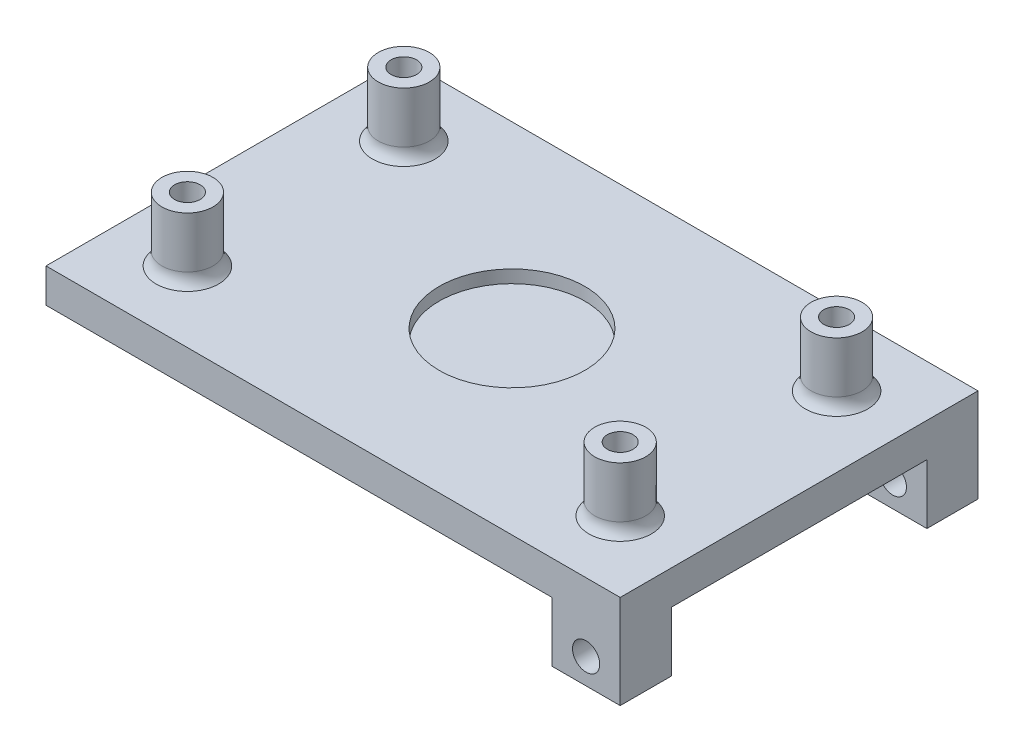
SolidWorks part; units mm, degrees
ref_plane "Front Plane" through (0, 0, 0) normal (0, 0, 1) x (1, 0, 0)
ref_plane "Top Plane" through (0, 0, 0) normal (0, 1, 0) x (1, 0, 0)
ref_plane "Right Plane" through (0, 0, 0) normal (1, 0, 0) x (0, 0, -1)
sketch "Sketch2" plane through (0, 0, 0) normal (0, 1, 0) x (1, 0, 0)
  line L1 (0, 0) -> (75.4, 0)
  line L2 (0, 0) -> (0, 50)
  line L3 (0, 50) -> (75.4, 50)
  line L4 (75.4, 0) -> (75.4, 50)
  dimension "D1" = 50
  dimension "D2" = 75.4
extrude "Boss-Extrude1" add sketch "Sketch2" along normal blind 3.5
sketch "Sketch3" plane through (0, 3.5, 0) normal (0, 1, 0) x (1, 0, 0)
  line L0 (0, 50) -> (0, 0) construction
  line L1 (75.4, 0) -> (75.4, 50) construction
  circle A0 centre (12.3, 37.7) radius 1.5
  circle A1 centre (12.3, 12.3) radius 1.5
  circle A2 centre (63.1, 37.7) radius 1.5
  circle A3 centre (63.1, 12.3) radius 1.5
  point P4 (0, 25)
  point P19 (75.4, 25)
  dimension "D1" = 3
  dimension "D3" = 12.7
  dimension "D4" = 0
  dimension "D5" = 50.8
  dimension "D2" = 0
  dimension "D6" = 12.7
  dimension "D7" = 12.7
extrude "Cut-Extrude1" cut sketch "Sketch3" against normal blind 4
sketch "Sketch4" plane through (0, 3.5, 0) normal (0, 1, 0) x (1, 0, 0)
  circle A0 centre (12.3, 37.7) radius 1.5
  circle A1 centre (12.3, 37.7) radius 3
  dimension "D1" = 6
extrude "Boss-Extrude2" add sketch "Sketch4" along normal blind 8
ref_plane "Plane1" through (37.7, 0, 0) normal (-1, 0, 0) x (0, 0, 1)
ref_plane "Plane2" through (0, 0, -25) normal (0, 0, 1) x (1, 0, 0)
mirror "Mirror1" about plane through (0, 0, -25) normal (0, 0, 1) of "Boss-Extrude2"
mirror "Mirror2" about plane through (37.7, 0, 0) normal (-1, 0, 0) of "Mirror1", "Boss-Extrude2"
fillet "Fillet1" radius 2 4 edges at (63.1, 3.5, -15.3) (63.1, 3.5, -34.7) (12.3, 3.5, -40.7) (12.3, 3.5, -15.3)
sketch "Sketch6" plane through (0, 0, 0) normal (0, -1, 0) x (1, 0, 0)
  line L4 (0, 0) -> (0, -50)
  line L5 (0, -50) -> (75.4, -50)
  line L6 (75.4, -50) -> (75.4, 0)
  line L7 (75.4, 0) -> (0, 0)
  line L8 (0, 0) -> (0, -50)
  line L9 (0, -50) -> (75.4, -50)
  line L10 (75.4, -50) -> (75.4, 0)
  line L11 (75.4, 0) -> (0, 0)
  dimension "D1" = 0
extrude "Boss-Extrude3" add sketch "Sketch6" against normal blind 4
sketch "Sketch8" plane through (0, 0, 0) normal (0, -1, 0) x (1, 0, 0)
  line L0 (37.7, 3.025) -> (37.7, -3.025) construction
  line L1 (8.7, -30) -> (12.7, -30)
  line L2 (8.7, -30) -> (8.7, -45)
  line L3 (8.7, -45) -> (12.7, -45)
  line L4 (12.7, -30) -> (12.7, -45)
  line L5 (12.7, -45) -> (62.7, -45)
  line L6 (12.7, -45) -> (12.7, -41)
  line L7 (12.7, -41) -> (62.7, -41)
  line L8 (62.7, -45) -> (62.7, -41)
  line L9 (3.025, -25) -> (-3.025, -25) construction
  dimension "D1" = 4
  dimension "D2" = 4
  dimension "D3" = 15
  dimension "D4" = 50
  dimension "D5" = 25
  dimension "D6" = 16
extrude "Boss-Extrude4" [suppressed] add sketch "Sketch8" along normal blind 6 contours L5 L8 L7 L6 | L3 L2 L1 L4
fillet "Fillet2" [suppressed] radius 1
fillet "Fillet3" [suppressed] radius 1
mirror "Mirror3" [suppressed] about plane through (0, 0, -25) normal (0, 0, 1)
sketch "Sketch9" plane through (0, 4, 0) normal (0, 1, 0) x (1, 0, 0)
  line L0 (37.7, 50) -> (37.7, 0) construction
  line L3 (0, 50) -> (75.4, 50) construction
  line L4 (75.4, 0) -> (0, 0) construction
  circle A0 centre (37.7, 25) radius 8.55
  dimension "D1" = 17.1
extrude "Cut-Extrude2" cut sketch "Sketch9" against normal blind 1.5
sketch "Sketch10" plane through (0, 0, 0) normal (0, -1, 0) x (1, 0, 0)
  line L0 (0, -25) -> (75.4, -25) construction
  line L1 (0, -50) -> (0, 0) construction
  line L2 (75.4, 0) -> (75.4, -50) construction
  circle A0 centre (17.6997, -25) radius 4.85
  dimension "D1" = 9.7
extrude "Cut-Extrude3" cut sketch "Sketch10" against normal blind 1.87
sketch "Sketch11" plane through (0, 1.87, 0) normal (0, -1, 0) x (1, 0, 0)
  circle A0 centre (17.6997, -25) radius 4
  dimension "D1" = 8
extrude "Cut-Extrude4" cut sketch "Sketch11" against normal blind 0.5
sketch "Sketch12" plane through (0, 0, 0) normal (0, -1, 0) x (1, 0, 0)
  line L0 (0, -50) -> (0, 0) construction
  line L1 (0, -27.5) -> (12.8497, -27.5)
  line L2 (0, -27.5) -> (0, -22.5)
  line L3 (0, -22.5) -> (12.8497, -22.5)
  line L4 (12.8497, -27.5) -> (12.8497, -22.5)
  line L5 (12.8497, -27.5) -> (13.5437, -27.5)
  line L6 (12.8497, -22.5) -> (13.5437, -22.5)
  circle A0 centre (17.6997, -25) radius 4.85 construction
  circle A1 centre (17.6997, -25) radius 4.85
  point P6 (0, -25)
  circle M5 centre (17.6997, -25) radius 4.85
  line M6 (0, 0) -> (0, -50)
  dimension "D1" = 2.5
  dimension "D2" = 5
extrude "Cut-Extrude6" cut sketch "Sketch12" against normal blind 1.87 contours L4 L5 M5 | L6 L4 M5 | L1 L4 L3 M6
sketch "Sketch13" [suppressed] plane through (0, 0, 0) normal (0, -1, 0) x (1, 0, 0)
  line L0 (12.7, -41) -> (61.7, -41) construction
  line L1 (23.4, -41) -> (75.4, -41)
  line L2 (23.4, -41) -> (23.4, -9)
  line L3 (23.4, -9) -> (75.4, -9)
  line L4 (75.4, -41) -> (75.4, -9)
  line L5 (75.4, 0) -> (75.4, -50) construction
  line L6 (12.7, -9) -> (61.7, -9) construction
  dimension "D1" = 52
extrude "Boss-Extrude5" [suppressed] add sketch "Sketch13" along normal blind 0.25
sketch "Sketch14" plane through (0, 0, 0) normal (0, -1, 0) x (1, 0, 0)
  line L1 (63.4, -4) -> (71.4, -4)
  line L2 (63.4, -4) -> (63.4, -10)
  line L3 (63.4, -10) -> (71.4, -10)
  line L4 (71.4, -4) -> (71.4, -10)
  line L6 (0, 0) -> (75.4, 0) construction
  line L7 (75.4, 0) -> (75.4, -50) construction
  dimension "D1" = 6
  dimension "D2" = 8
  dimension "D3" = 4
  dimension "D4" = 4
extrude "Boss-Extrude6" add sketch "Sketch14" along normal blind 8
sketch "Sketch15" plane through (0, 0, -10) normal (0, 0, -1) x (-1, 0, 0)
  line L0 (-67.4, -8) -> (-67.4, 0) construction
  line L1 (-63.4, -8) -> (-71.4, -8) construction
  line L2 (-63.4, 0) -> (-71.4, 0) construction
  circle A0 centre (-67.4, -4) radius 1.6
  dimension "D1" = 3.2
extrude "Cut-Extrude7" cut sketch "Sketch15" against normal blind 8
mirror "Mirror4" about plane through (0, 0, -25) normal (0, 0, 1) of "Cut-Extrude7", "Boss-Extrude6"
sketch "Sketch16" plane through (0, 0, 0) normal (0, -1, 0) x (1, 0, 0)
  line L51 (0, -50) -> (0, -27.5) construction
  line L52 (71.4, -4) -> (4, -4)
  line L53 (71.4, -4) -> (71.4, -46)
  line L54 (71.4, -46) -> (4, -46)
  line L55 (4, -4) -> (4, -46)
  line L56 (71.4, -4) -> (4, -46) construction
  line L57 (71.4, -46) -> (4, -4) construction
  line L58 (75.4, -50) -> (0, -50) construction
  line L59 (75.4, -50) -> (0, -50) construction
  line L60 (0, 0) -> (4, 0)
  line L61 (0, 0) -> (0, -50)
  line L62 (0, -50) -> (4, -50)
  line L63 (4, 0) -> (4, -50)
  point P69 (37.7, -25)
  line M7 (71.4, -40) -> (71.4, -46)
  line M8 (0, -50) -> (75.4, -50)
  line M9 (75.4, -50) -> (75.4, 0)
  line M11 (71.4, -4) -> (71.4, -10)
  line M14 (75.4, 0) -> (0, 0)
  line M15 (0, 0) -> (0, -22.5)
  line M16 (0, -22.5) -> (13.5437, -22.5)
  line M18 (13.5437, -27.5) -> (0, -27.5)
  line M19 (0, -27.5) -> (0, -50)
  line M25 (71.4, -46) -> (63.4, -46)
  line M26 (63.4, -4) -> (71.4, -4)
  dimension "D1" = 4
  dimension "D2" = 4
extrude "Cut-Extrude8" cut sketch "Sketch16" against normal blind 8 contours L63 L55 M18 M19 M8 | L61 L55 M16 M18 | L63 L55 M14 M15 M16 | L63 L52 L53 L54 M14 M26 M11 M7 M25 M8 M9
sketch "Sketch17" plane through (0, -8, 0) normal (0, -1, 0) x (1, 0, 0)
  line L0 (63.4, -40) -> (63.4, -46) construction
  line L1 (63.4, -46) -> (71.4, -46) construction
  line L2 (71.4, -46) -> (71.4, -40) construction
  line L3 (71.4, -40) -> (63.4, -40) construction
  line L4 (63.4, -4) -> (63.4, -10) construction
  line L5 (63.4, -10) -> (71.4, -10) construction
  line L6 (71.4, -10) -> (71.4, -4) construction
  line L7 (71.4, -4) -> (63.4, -4) construction
  line L8 (63.4, -40) -> (63.4, -46)
  line L9 (63.4, -46) -> (71.4, -46)
  line L10 (71.4, -46) -> (71.4, -40)
  line L11 (71.4, -40) -> (63.4, -40)
  line L12 (63.4, -4) -> (63.4, -10)
  line L13 (63.4, -10) -> (71.4, -10)
  line L14 (71.4, -10) -> (71.4, -4)
  line L15 (71.4, -4) -> (63.4, -4)
extrude "Cut-Extrude9" cut sketch "Sketch17" against normal blind 1
